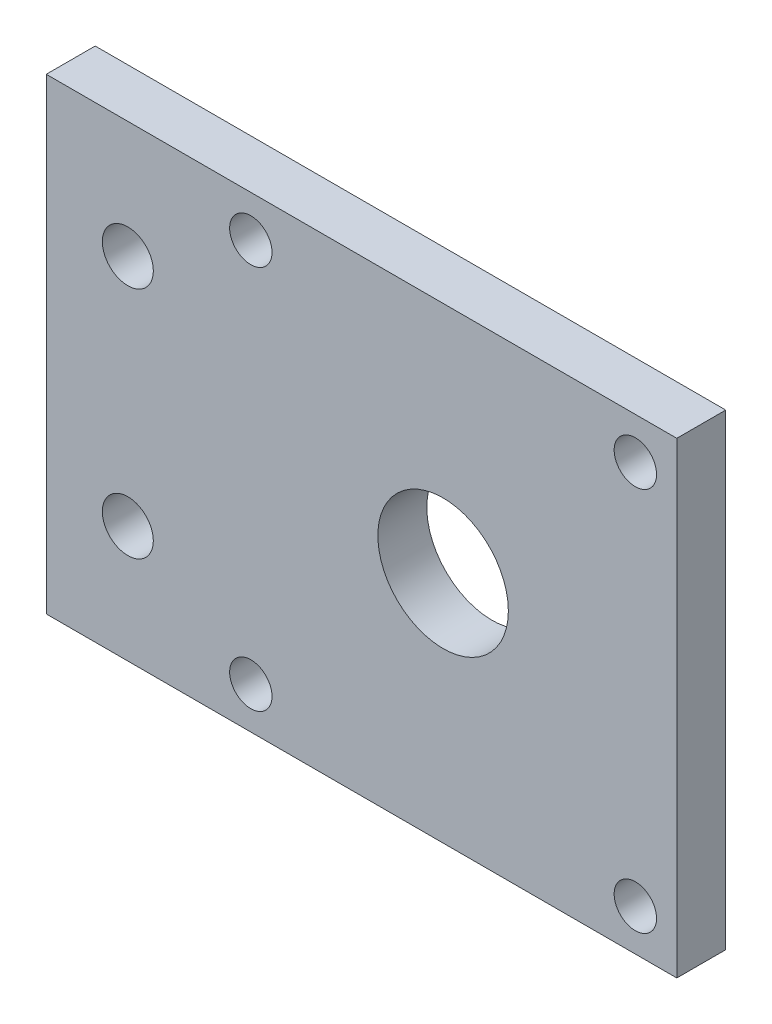
SolidWorks part; units mm, degrees
ref_plane "Front Plane" through (0, 0, 0) normal (0, 0, 1) x (1, 0, 0)
ref_plane "Top Plane" through (0, 0, 0) normal (0, 1, 0) x (1, 0, 0)
ref_plane "Right Plane" through (0, 0, 0) normal (1, 0, 0) x (0, 0, -1)
sketch "Sketch1" plane through (0, 0, 0) normal (0, 0, 1) x (1, 0, 0)
  line L1 (-38.65, -28.65) -> (38.65, -28.65)
  line L2 (-38.65, -28.65) -> (-38.65, 28.65)
  line L3 (-38.65, 28.65) -> (38.65, 28.65)
  line L4 (38.65, -28.65) -> (38.65, 28.65)
  line L5 (-38.65, -28.65) -> (38.65, 28.65) construction
  line L6 (-38.65, 28.65) -> (38.65, -28.65) construction
  point P0 (0, 0)
  dimension "D1" = 57.3
  dimension "D2" = 77.3
extrude "Boss-Extrude1" add sketch "Sketch1" along normal blind 6
sketch "Sketch2" plane through (0, 0, 6) normal (0, 0, 1) x (1, 0, 0)
  line L0 (-18.65, 28.65) -> (-18.65, -28.65) construction
  line L1 (-18.65, 0) -> (10, 0) construction
  line L2 (-28.65, 28.65) -> (-28.65, -28.65) construction
  line L3 (33.57, -23.57) -> (-13.57, -23.57) construction
  line L4 (38.65, 28.65) -> (-38.65, 28.65) construction
  line L5 (-38.65, -28.65) -> (38.65, -28.65) construction
  line L6 (-38.65, 28.65) -> (-38.65, -28.65) construction
  line L7 (33.57, -23.57) -> (33.57, 23.57) construction
  line L8 (33.57, 23.57) -> (-13.57, 23.57) construction
  line L9 (-13.57, -23.57) -> (-13.57, 23.57) construction
  line L10 (33.57, -23.57) -> (-13.57, 23.57) construction
  line L11 (33.57, 23.57) -> (-13.57, -23.57) construction
  circle A0 centre (10, 0) radius 8
  circle A1 centre (-13.57, 23.57) radius 2.6
  circle A2 centre (33.57, 23.57) radius 2.6
  circle A3 centre (33.57, -23.57) radius 2.6
  circle A4 centre (-13.57, -23.57) radius 2.6
  point P22 (-28.65, 14.325)
  point P23 (-28.65, 0)
  point P24 (-28.65, -14.325)
  dimension "D3" = 16
  dimension "D6" = 5.2
  dimension "D7" = 5.2
  dimension "D8" = 5.2
  dimension "D9" = 5.2
  dimension "D1" = 20
  dimension "D2" = 28.65
  dimension "D4" = 47.14
  dimension "D5" = 47.14
  dimension "D10" = 10
extrude "Cut-Extrude1" cut sketch "Sketch2" against normal blind 6
hole_wizard "Tap Drill for M6 Helicoil1" positions "3DSketch2" profile "Sketch5" hole size "M6x1.0" standard "ANSI Metric"
sketch3d "3DSketch2"
  point P0 (-28.65, 14.325, 6)
  point P3 (-28.65, -14.325, 6)
sketch "Sketch5" plane through (-28.65, 14.325, 6) normal (1, 0, 0) x (0, -1, 0)
  line L0 (0, 0) -> (0, 21.8777)
  line L1 (0, 21.8777) -> (3.125, 20)
  line L2 (3.125, 20) -> (3.125, 0)
  line L5 (3.125, 0) -> (0, 0)
  line L10 (0, 21.8777) -> (-3.125, 20) construction
  line L11 (0, -6.35) -> (0, 107.95) construction
  dimension "Hole Dia." = 6.25
  dimension "Hole Depth" = 20
  dimension "Drill Angle" = 118
